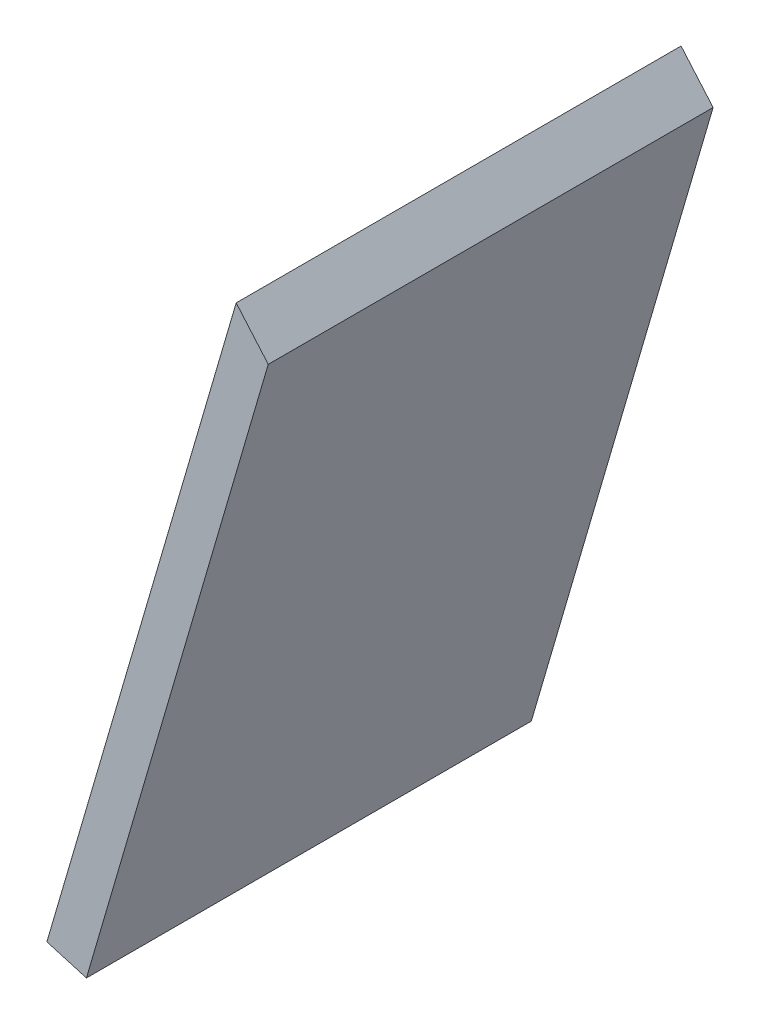
SolidWorks part; units mm, degrees
ref_plane "Front Plane" through (0, 0, 0) normal (0, 0, 1) x (1, 0, 0)
ref_plane "Top Plane" through (0, 0, 0) normal (0, 1, 0) x (1, 0, 0)
ref_plane "Right Plane" through (0, 0, 0) normal (1, 0, 0) x (0, 0, -1)
sketch "Sketch1" plane through (0, 0, 413.8923) normal (0, 0, 1) x (1, 0, 0)
  line L1 (-272.519, -127.1258) -> (-268.63, -131.6443)
  line L2 (-272.519, -127.1258) -> (-330.7143, -326.3392)
  line L5 (-268.63, -131.6443) -> (-324.8429, -324.0715)
  line L7 (-330.7143, -326.3392) -> (-324.8429, -324.0715)
  line L9 (-260.9091, -87.3827) -> (-368.3045, -455.0173) construction
  line L10 (-256.1097, -88.7847) -> (-363.5051, -456.4194) construction
  line L11 (-301.1819, -47.3631) -> (-211.2536, -280.2) construction
  line L12 (-211.2536, -280.2) -> (-529.2589, -403.0228) construction
extrude "Boss-Extrude1" add sketch "Sketch1" along normal up to surface (208.2958 mm away)
sketch "Sketch2" plane through (-212.0754, 61.9526, 0) normal (0.9599, -0.2804, 0) x (0, 0, -1)
  line L0 (-413.8923, -280.365) -> (-622.1881, -280.365)
  line L1 (-413.8923, -280.365) -> (-413.8923, -405.9812)
  line L2 (-622.1881, -280.365) -> (-622.1881, -405.9812)
  line L3 (-413.8923, -405.9812) -> (-622.1881, -405.9812)
  line L5 (-622.1881, -402.1581) -> (-622.1881, -201.6884) construction
  line L7 (-408.8923, -280.365) -> (-411.8923, -280.365) construction
  line L8 (-413.8923, -402.1581) -> (-413.8923, -201.6884) construction
  line L9 (-622.1881, -405.9812) -> (-413.8923, -405.9812) construction
extrude "Cut-Extrude1" cut sketch "Sketch2" against normal blind 20
sketch "Sketch3" plane through (0, 0, 568.2023) normal (0, 0, -1) x (-1, 0, 0)
  circle A0 centre (268.1265, -164.0601) radius 77.5
  circle A1 centre (268.1265, -164.0601) radius 77.5 construction
extrude "Cut-Extrude2" cut sketch "Sketch3" along normal through all
